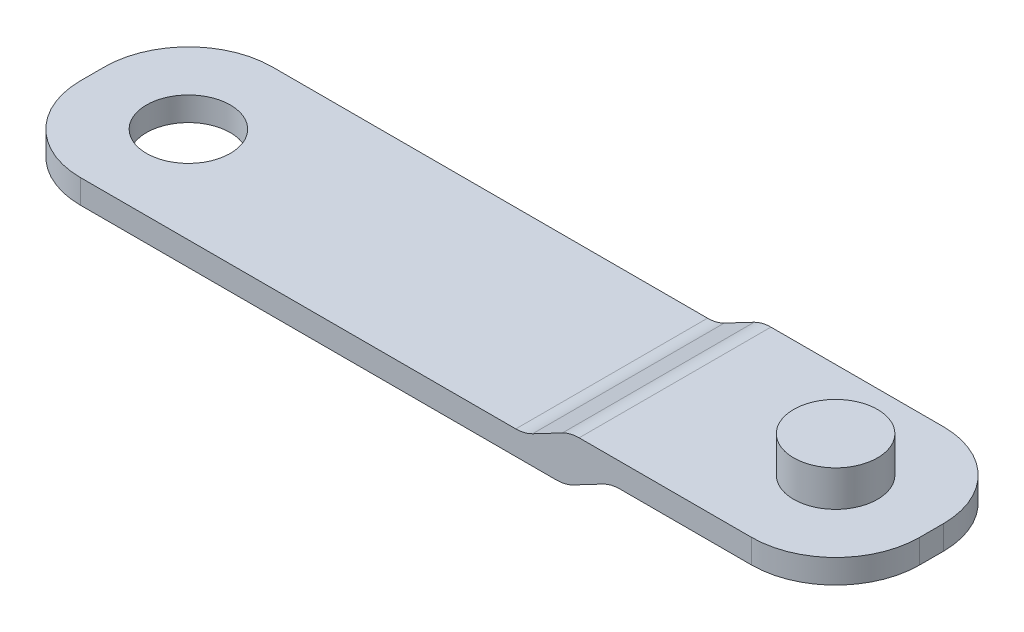
SolidWorks part; units mm, degrees
ref_plane "Front Plane" through (0, 0, 0) normal (0, 0, 1) x (1, 0, 0)
ref_plane "Top Plane" through (0, 0, 0) normal (0, 1, 0) x (1, 0, 0)
ref_plane "Right Plane" through (0, 0, 0) normal (1, 0, 0) x (0, 0, -1)
sketch "Sketch1" plane through (0, 0, 0) normal (0, 1, 0) x (1, 0, 0)
  line L0 (-151.848, 0) -> (151.848, 0) construction
  line L1 (0, 80.646) -> (0, -80.646) construction
  line L2 (-12.6651, 7.9317) -> (-27.591, 7.9319)
  line L3 (-34.591, 0.9319) -> (-34.5911, -1.0681)
  line L4 (-27.5911, -8.0681) -> (-12.6653, -8.0683)
  line L5 (-12.6653, -8.0683) -> (28.4089, -8.0688)
  line L6 (35.4089, -1.0689) -> (35.409, 0.9311)
  line L7 (28.409, 7.9312) -> (-12.6651, 7.9317)
  arc A0 (27.409, 3.4312) -> (27.4089, -3.5688) centre (27.409, -0.0688) ccw
  arc A1 (27.4089, -3.5688) -> (27.409, 3.4312) centre (27.409, -0.0688) ccw
  arc A2 (-30.091, -0.0681) -> (-23.091, -0.0682) centre (-26.591, -0.0682) ccw
  arc A3 (-23.091, -0.0682) -> (-30.091, -0.0681) centre (-26.591, -0.0682) ccw
  arc A4 (-27.591, 7.9319) -> (-34.591, 0.9319) centre (-27.591, 0.9319) ccw
  arc A5 (-34.5911, -1.0681) -> (-27.5911, -8.0681) centre (-27.5911, -1.0681) ccw
  arc A6 (28.4089, -8.0688) -> (35.4089, -1.0689) centre (28.4089, -1.0688) ccw
  arc A7 (35.409, 0.9311) -> (28.409, 7.9312) centre (28.409, 0.9312) ccw
  point P3 (0.2549, -0.3298)
  point P4 (0, 0)
  point P8 (0, 0)
  point P9 (0.2549, -0.3298)
  dimension "D1" = 8
extrude "Boss-Extrude1" add sketch "Sketch1" along normal blind 4 contours L6 A7 L7 L2 A4 L3 A5 L4 L5 A6 A1 A0 A3 A2 | A0 A1
sketch "Sketch4" plane through (-0.0001, 0, 8.0685) normal (0, 0, 1) x (1, 0, 0)
  line L0 (0, 12.1207) -> (0, -12.1207) construction
  line L2 (-44.2001, 2) -> (44.2001, 2) construction
  line L3 (-27.591, 0) -> (28.409, 0) construction
  line L4 (35.409, 4) -> (35.409, 2)
  line L5 (35.409, 4) -> (35.409, 0) construction
  line L6 (35.409, 2) -> (16.665, 2)
  line L7 (16.665, 2) -> (12.8585, 0)
  line L8 (12.8585, 0) -> (-34.591, 0)
  line L9 (-34.591, 0) -> (-34.591, 2)
  line L10 (-34.591, 4) -> (-34.591, 0) construction
  line L11 (-34.591, 2) -> (9.4649, 2)
  line L12 (9.4649, 2) -> (13.2714, 4)
  line L13 (-27.591, 4) -> (28.409, 4) construction
  line L14 (13.2714, 4) -> (35.409, 4)
  line L15 (12.8585, 0) -> (35.409, 0)
  line L16 (35.409, 0) -> (35.409, 2)
  line L17 (-34.591, 2) -> (-34.591, 4)
  line L18 (-34.591, 4) -> (13.2714, 4)
  point P4 (0, 0)
  point P8 (0, 2)
  line M3 (-27.591, 0) -> (28.409, 0)
  line M4 (28.409, 0) -> (28.409, 4)
  line M5 (28.409, 4) -> (-27.591, 4)
  line M6 (-27.591, 4) -> (-27.591, 0)
  dimension "D1" = 2
  dimension "D2" = 4.3
extrude "Cut-Extrude2" cut sketch "Sketch4" against normal through all contours L11 L12 M5 M6 | L18 L17 L11 M6 | L6 L7 M3 M4 | L15 L16 L6 M4
fillet "Fillet1" radius 3 4 edges at (13.2714, 4, 0.0686) (9.4649, 2, 0.0686) (12.8585, 0, 0.0686) (16.665, 2, 0.0686)
sketch "Sketch5" plane through (0, 4, 0) normal (0, 1, 0) x (1, 0, 0)
  circle A0 centre (27.409, -0.0688) radius 3.5
extrude "Boss-Extrude2" add sketch "Sketch5" along normal blind 3
